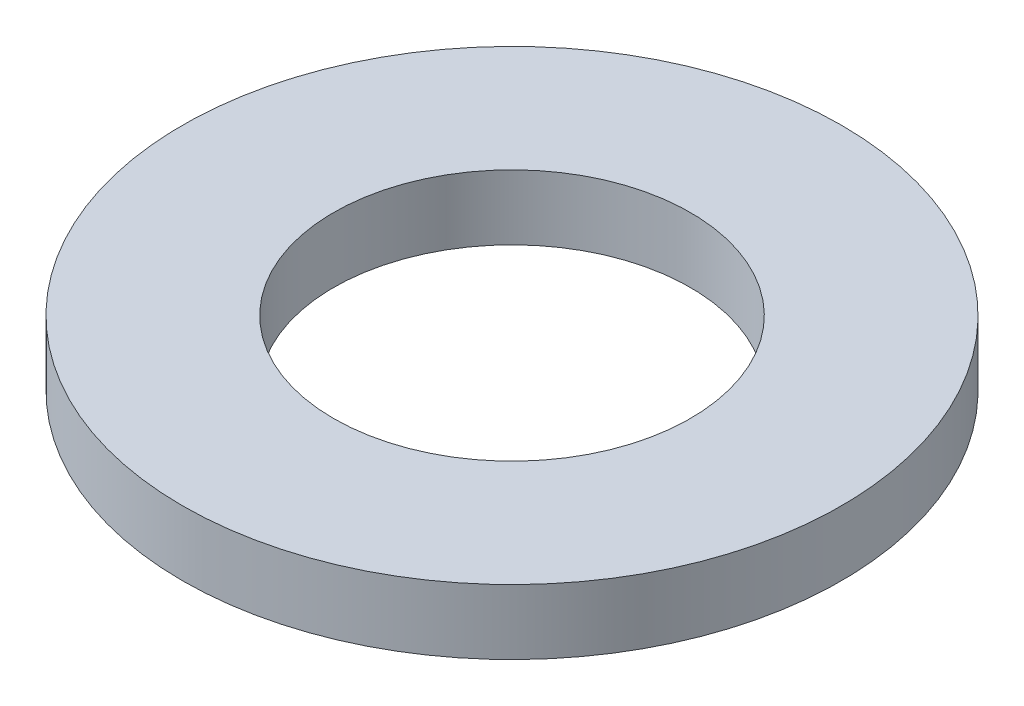
SolidWorks part; units mm, degrees
material "ABS"
ref_plane "Front Plane" through (0, 0, 0) normal (0, 0, 1) x (1, 0, 0)
ref_plane "Top Plane" through (0, 0, 0) normal (0, 1, 0) x (1, 0, 0)
ref_plane "Right Plane" through (0, 0, 0) normal (1, 0, 0) x (0, 0, -1)
sketch "Sketch1" plane through (0, 0, 0) normal (0, 1, 0) x (1, 0, 0)
  circle A0 centre (0, 0) radius 20.6
  circle A1 centre (0, 0) radius 38.05
  dimension "D1" = 41.2
  dimension "D2" = 76.1
extrude "Boss-Extrude1" add sketch "Sketch1" along normal blind 7.5
